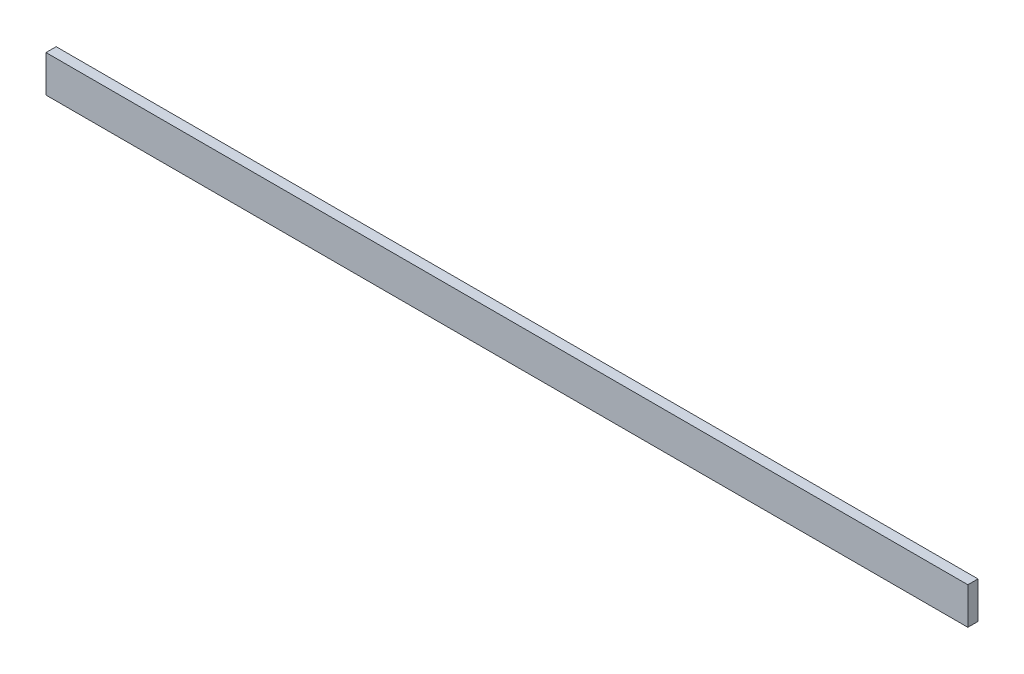
SolidWorks part; units mm, degrees
ref_plane "Face" through (0, 0, 0) normal (0, 0, 1) x (1, 0, 0)
ref_plane "Dessus" through (0, 0, 0) normal (0, 1, 0) x (1, 0, 0)
ref_plane "Droite" through (0, 0, 0) normal (1, 0, 0) x (0, 0, -1)
sketch "Esquisse1" plane through (0, 0, 0) normal (0, 0, 1) x (1, 0, 0)
  line L1 (0, 0) -> (2000, 0)
  line L2 (0, 0) -> (0, 80)
  line L3 (0, 80) -> (2000, 80)
  line L4 (2000, 0) -> (2000, 80)
  dimension "D1" = 2000
  dimension "D2" = 80
extrude "Extrusion1" add sketch "Esquisse1" along normal blind 22
